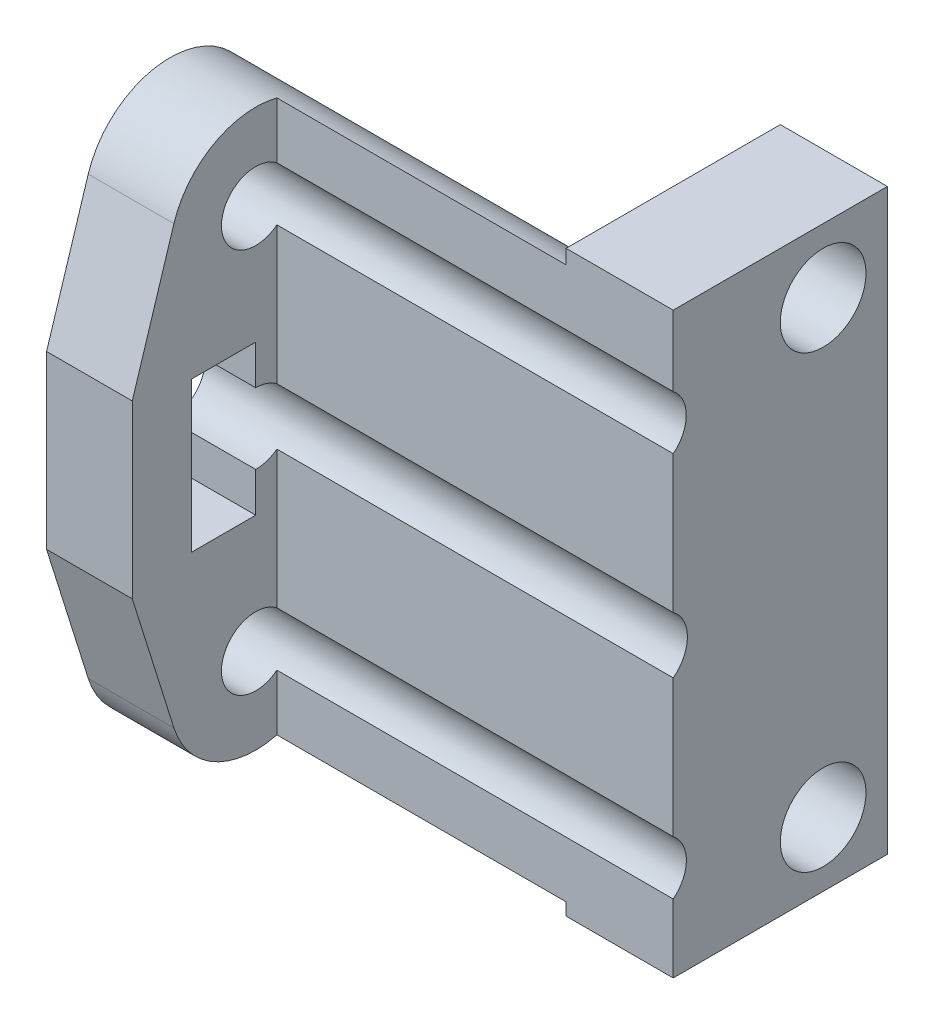
SolidWorks part; units mm, degrees
ref_plane "Front Plane" through (0, 0, 0) normal (0, 0, 1) x (1, 0, 0)
ref_plane "Top Plane" through (0, 0, 0) normal (0, 1, 0) x (1, 0, 0)
ref_plane "Right Plane" through (0, 0, 0) normal (1, 0, 0) x (0, 0, -1)
sketch "Esboço1" plane through (0, 0, 0) normal (0, 0, 1) x (1, 0, 0)
  line L1 (0, 215.9684) -> (5, 215.9684)
  line L2 (0, 215.9684) -> (0, 188.9684)
  line L3 (0, 188.9684) -> (5, 188.9684)
  line L4 (5, 215.9684) -> (5, 188.9684)
  point P12 (0, 0)
extrude "Ressalto-extrusão1" add sketch "Esboço1" along normal blind 4 and the other way blind 6
sketch "Esboço2" plane through (0, 0, 0) normal (-1, 0, 0) x (0, 0, 1)
  line L8 (-6, 215.9684) -> (-6, 188.9684)
  line L9 (-6, 188.9684) -> (4, 188.9684)
  line L10 (4, 188.9684) -> (4, 215.9684)
  line L11 (4, 215.9684) -> (-6, 215.9684)
  line L12 (0, 215.9684) -> (0, 188.9684)
  line L13 (0, 188.9684) -> (4, 188.9684)
  line L14 (4, 188.9684) -> (4, 215.9684)
  line L15 (4, 215.9684) -> (0, 215.9684)
  dimension "D2" = 4
  dimension "D1" = 0
extrude "Ressalto-extrusão2" add sketch "Esboço2" along normal blind 17.5
sketch "Esboço3" plane through (0, 0, 4) normal (0, 0, 1) x (1, 0, 0)
  line L0 (-17.5, 188.9684) -> (5, 188.9684) construction
  line L1 (-17.5, 215.9684) -> (-13.5, 215.9684)
  line L2 (-17.5, 215.9684) -> (-17.5, 188.9684)
  line L3 (-17.5, 188.9684) -> (-13.5, 188.9684)
  line L4 (-13.5, 215.9684) -> (-13.5, 188.9684)
  dimension "D1" = 4
extrude "Ressalto-extrusão3" add sketch "Esboço3" along normal up to vertex (6.7523 mm away)
sketch "Esboço4" plane through (-17.5, 0, 0) normal (-1, 0, 0) x (0, 0, 1)
  line L6 (10.7523, 206.4233) -> (10.7523, 215.9684)
  line L7 (10.7523, 215.9684) -> (0, 215.9684)
  line L10 (10.7523, 198.4233) -> (10.7523, 188.9684)
  line L11 (10.7523, 188.9684) -> (0, 188.9684)
  line L12 (-0.7757, 198.4233) -> (1.1717, 192.2243)
  line L13 (-0.7757, 206.4233) -> (-0.7757, 198.4233)
  line L14 (1.172, 212.6211) -> (-0.7757, 206.4233)
  line L15 (10.7523, 206.4233) -> (8.8084, 212.6193)
  line L16 (10.7523, 198.4233) -> (10.7523, 206.4233)
  line L17 (8.8048, 192.2242) -> (10.7523, 198.4233)
  line L18 (0, 195.9541) -> (1.1717, 192.2243)
  line L20 (1.172, 212.6211) -> (0, 208.8916)
  line L21 (10.7523, 206.4233) -> (8.8084, 212.6193)
  line L23 (8.8048, 192.2242) -> (10.7523, 198.4233)
  line L55 (0, 188.9684) -> (0, 195.9541)
  line L56 (0, 208.8916) -> (0, 215.9684)
  arc A4 (1.1717, 192.2243) -> (8.8048, 192.2242) centre (4.9883, 193.4232) ccw
  arc A5 (8.8084, 212.6193) -> (1.172, 212.6211) centre (4.9899, 211.4213) ccw
  arc A6 (1.1717, 192.2243) -> (8.8048, 192.2242) centre (4.9883, 193.4232) ccw
  arc A7 (8.8084, 212.6193) -> (1.172, 212.6211) centre (4.9899, 211.4213) ccw
  point P3 (0, 0)
  dimension "D1" = 0
extrude "Corte-extrusão1" cut sketch "Esboço4" against normal blind 17.5
sketch "Esboço5" plane through (-17.5, 0, 0) normal (-1, 0, 0) x (0, 0, 1)
  line L0 (4.9893, 200.7724) -> (4.9893, 198.9233)
  line L1 (4.9893, 205.9233) -> (7.9893, 205.9233)
  line L2 (4.9893, 205.9233) -> (4.9893, 204.0743)
  line L3 (4.9893, 198.9233) -> (7.9893, 198.9233)
  line L4 (7.9893, 205.9233) -> (7.9893, 198.9233)
  circle A8 centre (4.9899, 211.4213) radius 1.5982
  circle A9 centre (4.9899, 211.4213) radius 1.5982
  circle A11 centre (4.9893, 202.4233) radius 1.6509
  arc A12 (4.9893, 204.0743) -> (4.9893, 200.7724) centre (4.9893, 202.4233) ccw
  circle A13 centre (4.9893, 202.4233) radius 3.5 construction
  circle A14 centre (4.9883, 193.4232) radius 1.601
  circle A15 centre (4.9883, 193.4232) radius 1.601
  dimension "D4" = 3
  dimension "D1" = 0
  dimension "D2" = 0
  dimension "D3" = 0
extrude "Corte-extrusão2" cut sketch "Esboço5" against normal through all
sketch "Esboço6" plane through (0, 0, 0) normal (-1, 0, 0) x (0, 0, 1)
  line L0 (-6, 202.4684) -> (16.4895, 202.4684) construction
  line L1 (-6, 215.9684) -> (-6, 188.9684) construction
  line L2 (-6, 215.9684) -> (4, 215.9684) construction
  circle A0 centre (-3, 212.9684) radius 2
  circle A1 centre (-3, 191.9684) radius 2
  dimension "D1" = 4
  dimension "D2" = 3
  dimension "D3" = 3
extrude "Corte-extrusão3" cut sketch "Esboço6" against normal blind 14
